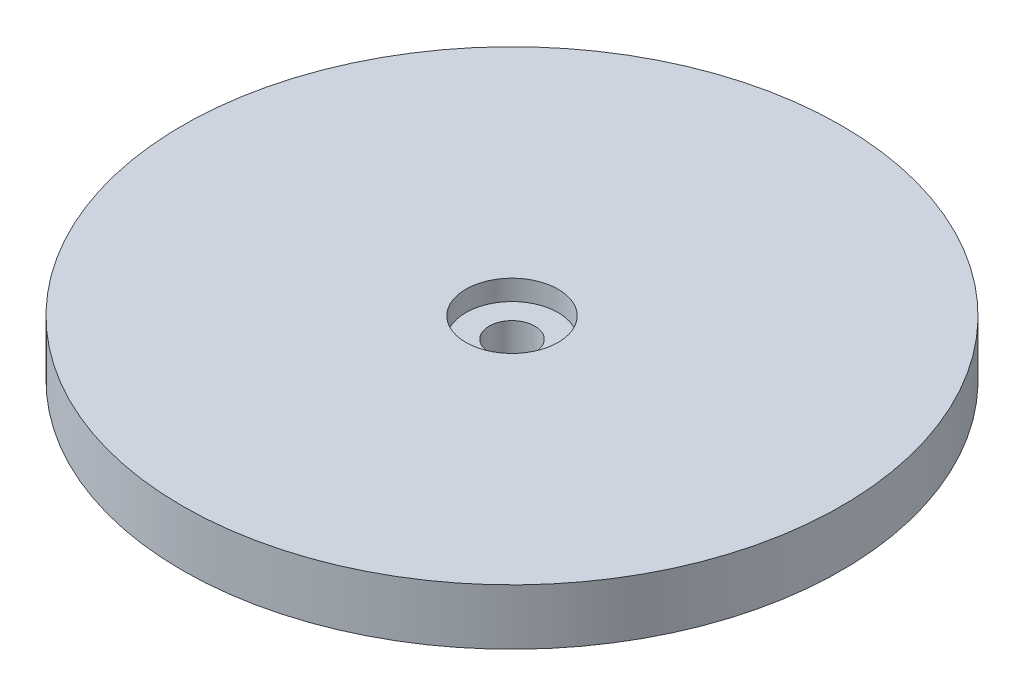
SolidWorks part; units mm, degrees
ref_plane "Front Plane" through (0, 0, 0) normal (0, 0, 1) x (1, 0, 0)
ref_plane "Top Plane" through (0, 0, 0) normal (0, 1, 0) x (1, 0, 0)
ref_plane "Right Plane" through (0, 0, 0) normal (1, 0, 0) x (0, 0, -1)
sketch "Sketch2" plane through (0, 0, 0) normal (0, 1, 0) x (1, 0, 0)
  circle A0 centre (0, 0) radius 65
  dimension "D1" = 130
extrude "Boss-Extrude1" add sketch "Sketch2" along normal blind 11
sketch "Sketch3" plane through (0, 11, 0) normal (0, 1, 0) x (1, 0, 0)
  circle A1 centre (0, 0) radius 9.1
  dimension "D2" = 18.2
extrude "Cut-Extrude2" cut sketch "Sketch3" against normal blind 4
sketch "Sketch4" plane through (0, 7, 0) normal (0, 1, 0) x (1, 0, 0)
  circle A0 centre (0, 0) radius 4.5
  dimension "D1" = 9
extrude "Cut-Extrude4" cut sketch "Sketch4" against normal blind 20
sketch "Sketch5" plane through (0, 11, 0) normal (0, 1, 0) x (1, 0, 0)
  circle A0 centre (0, 0) radius 41.25
  circle A1 centre (0, 0) radius 17.5
  dimension "D1" = 82.5
  dimension "D2" = 35
